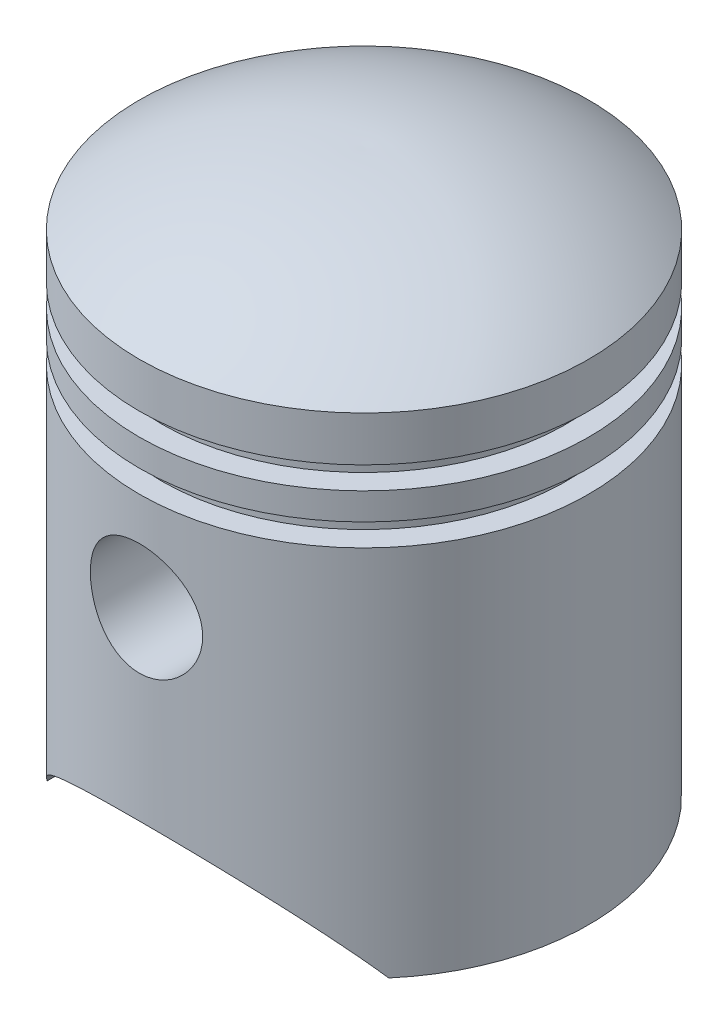
SolidWorks part; units mm, degrees
material "Nickel"
ref_plane "Front Plane" through (0, 0, 0) normal (0, 0, 1) x (1, 0, 0)
ref_plane "Top Plane" through (0, 0, 0) normal (0, 1, 0) x (1, 0, 0)
ref_plane "Right Plane" through (0, 0, 0) normal (1, 0, 0) x (0, 0, -1)
sketch "Sketch1" plane through (0, 0, 0) normal (0, 0, 1) x (1, 0, 0)
  line L0 (25, 0) -> (25, 41.5)
  line L1 (25, 49.5) -> (22.5, 49.5)
  line L2 (22.5, 49.5) -> (22.5, 47)
  line L3 (22.5, 47) -> (25, 47)
  line L4 (25, 44) -> (22.5, 44)
  line L5 (22.5, 44) -> (22.5, 41.5)
  line L6 (22.5, 41.5) -> (25, 41.5)
  line L7 (25, 49.5) -> (25, 54.5)
  line L8 (25, 44) -> (25, 47)
  line L9 (23, 0) -> (23, 39.5)
  line L10 (20.5, 39.5) -> (23, 39.5)
  line L11 (20.5, 45.5) -> (20.5, 39.5)
  line L12 (20.5, 45.5) -> (20.5, 45.5)
  line L13 (20.5, 45.5) -> (20.5, 45.5)
  line L14 (20.5, 45.5) -> (20.5, 45.5)
  line L15 (20.5, 51.5) -> (20.5, 45.5)
  line L16 (23, 51.5) -> (20.5, 51.5)
  line L17 (23, 51.5) -> (23, 53.4845)
  line L18 (25, 0) -> (23, 0)
  line L19 (0, 62.5) -> (0, 60.4994)
  arc A0 (25, 54.5) -> (0, 62.5) centre (0.9839, 22.5121) ccw
  arc A1 (23, 53.4845) -> (0, 60.4994) centre (0.9839, 22.5121) ccw
  arc A2 (23, 53.4845) -> (0.0492, 60.5006) centre (0.9839, 22.5121) ccw construction
  dimension "D4" = 40
  dimension "D1" = 62.5
  dimension "D2" = 25
  dimension "D3" = 54.5
  dimension "D5" = 5
  dimension "D6" = 2.5
  dimension "D7" = 2.5
  dimension "D8" = 3
  dimension "D9" = 2.5
  dimension "D10" = 2
revolve "Revolve1" add sketch "Sketch1" angle 360 about L19
sketch "Sketch2" plane through (0, 0, 0) normal (0, 0, 1) x (1, 0, 0)
  line L0 (-25, 0) -> (25, 0) construction
  line L1 (-19, 0) -> (19, 0)
  circle A0 centre (0, 30.5) radius 6.25
  arc A1 (-19, 0) -> (19, 0) centre (0, -13.05) cw
  point P10 (0, 10)
  dimension "D1" = 12.5
  dimension "D2" = 32
  dimension "D3" = 38
  dimension "D4" = 10
extrude "Cut-Extrude1" cut sketch "Sketch2" against normal through all both and the other way through all
sketch "Sketch3" plane through (0, 0, 0) normal (0, 0, 1) x (1, 0, 0)
  circle A0 centre (0, 30.5) radius 7.25
  circle A1 centre (0, 30.5) radius 6.25 construction
  circle A2 centre (0, 30.5) radius 6.25
  dimension "D1" = 14.5
extrude "Boss-Extrude2" add sketch "Sketch3" along normal up to surface (11.9257 mm away) from offset 12
mirror "Mirror1" about plane through (0, 0, 0) normal (0, 0, 1) of "Boss-Extrude2"
